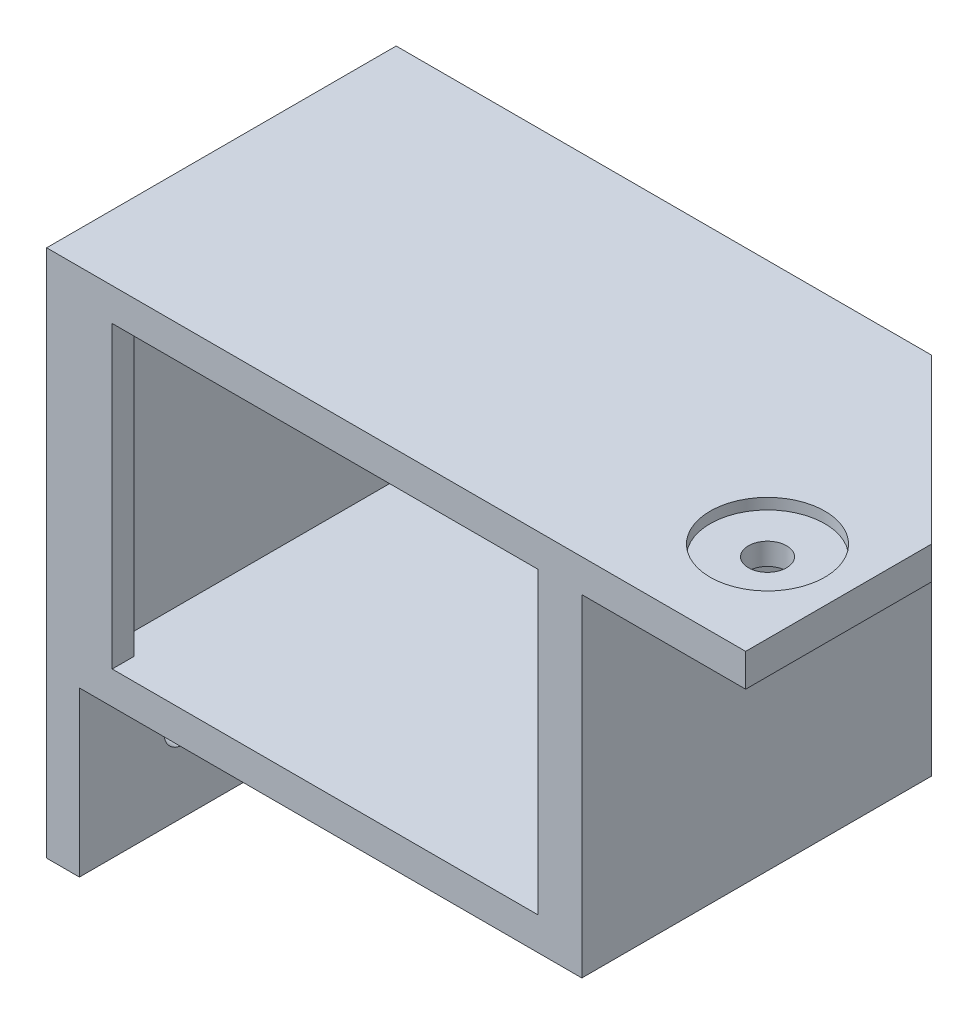
SolidWorks part; units mm, degrees
ref_plane "Plano frontal" through (0, 0, 0) normal (0, 0, 1) x (1, 0, 0)
ref_plane "Plano superior" through (0, 0, 0) normal (0, 1, 0) x (1, 0, 0)
ref_plane "Plano direito" through (0, 0, 0) normal (1, 0, 0) x (0, 0, -1)
sketch "Esboço1" plane through (0, 0, 0) normal (0, 0, 1) x (1, 0, 0)
  line L0 (0, 0) -> (64, 0)
  line L1 (64, 0) -> (64, -3)
  line L2 (64, -3) -> (49, -3)
  line L3 (49, -3) -> (49, -33.4)
  line L4 (49, -33.4) -> (3, -33.4)
  line L5 (3, -33.4) -> (3, -48.4)
  line L6 (3, -48.4) -> (0, -48.4)
  line L7 (0, -48.4) -> (0, 0)
  line L9 (6, -3) -> (45, -3)
  line L10 (6, -3) -> (6, -30.4)
  line L11 (6, -30.4) -> (45, -30.4)
  line L12 (45, -3) -> (45, -30.4)
  dimension "D1" = 3
  dimension "D2" = 15
  dimension "D3" = 46
  dimension "D4" = 39
  dimension "D5" = 4
  dimension "D6" = 3
  dimension "D7" = 27.4
extrude "Ressalto-extrusão1" add sketch "Esboço1" along normal blind 32
sketch "Esboço2" plane through (0, 0, 0) normal (0, 0, -1) x (-1, 0, 0)
  line L0 (-6, -3) -> (-6, -30.4) construction
  line L1 (-47, -3) -> (-4, -3)
  line L2 (-47, -3) -> (-47, -30.4)
  line L3 (-47, -30.4) -> (-4, -30.4)
  line L4 (-4, -3) -> (-4, -30.4)
  line L5 (-45, -30.4) -> (-45, -3) construction
  line L6 (-6, -30.4) -> (-45, -30.4) construction
  line L7 (-45, -3) -> (-6, -3) construction
  dimension "D1" = 2
  dimension "D2" = 2
extrude "Corte-extrusão1" cut sketch "Esboço2" against normal offset from surface (30 mm away) 2 up to face at (29, -21.2, 32)
sketch "Esboço3" plane through (0, -3, 0) normal (0, -1, 0) x (1, 0, 0)
  line L0 (49, 32) -> (64, 32) construction
  circle A0 centre (56.5, 22.5) radius 1.75
  point P4 (56.5, 32)
  dimension "D2" = 3.5
  dimension "D1" = 9.5
extrude "Corte-extrusão2" cut sketch "Esboço3" against normal blind 6
sketch "Esboço4" plane through (3, 0, 0) normal (1, 0, 0) x (0, 0, -1)
  line L0 (-32, -48.4) -> (-32, -33.4) construction
  circle A0 centre (-22.5, -40.9) radius 1.75
  point P4 (-32, -40.9)
  point P5 (0, 0)
  dimension "D1" = 3.5
  dimension "D2" = 9.5
extrude "Corte-extrusão3" cut sketch "Esboço4" against normal blind 6
chamfer "Chanfro1" distance 15 distance2 15 2 edges at (1.5, -48.4, 0) (64, -1.5, 0)
sketch "Esboço5" plane through (0, 0, 0) normal (0, 1, 0) x (1, 0, 0)
  circle A0 centre (56.5, -22.5) radius 5.25
  dimension "D1" = 10.5
extrude "Corte-extrusão4" cut sketch "Esboço5" against normal blind 1
sketch "Esboço6" plane through (0, 0, 0) normal (-1, 0, 0) x (0, 0, 1)
  circle A0 centre (22.5, -40.9) radius 5.25
  dimension "D1" = 10.5
extrude "Corte-extrusão5" cut sketch "Esboço6" against normal blind 1
